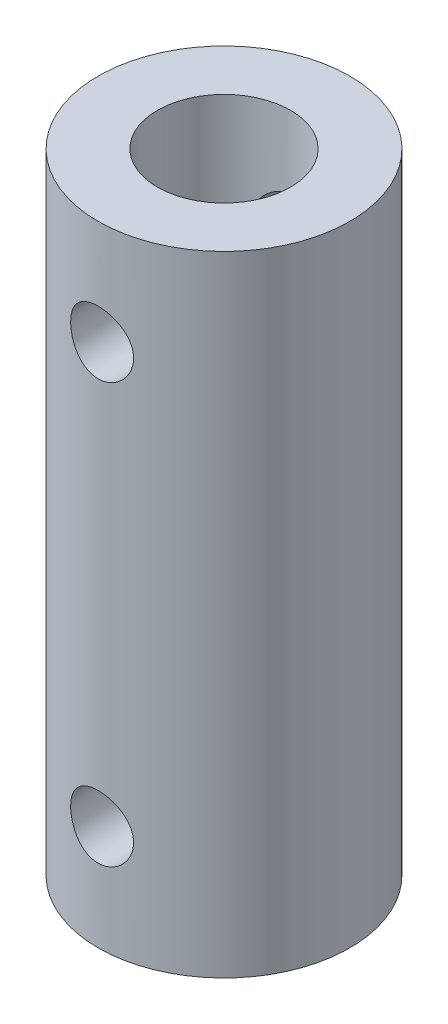
SolidWorks part; units mm, degrees
ref_plane "Front Plane" through (0, 0, 0) normal (0, 0, 1) x (1, 0, 0)
ref_plane "Top Plane" through (0, 0, 0) normal (0, 1, 0) x (1, 0, 0)
ref_plane "Right Plane" through (0, 0, 0) normal (1, 0, 0) x (0, 0, -1)
sketch "Sketch1" plane through (0, 0, 0) normal (0, 1, 0) x (1, 0, 0)
  circle A0 centre (0, 0) radius 6
  dimension "D1" = 12
extrude "Boss-Extrude1" add sketch "Sketch1" along normal blind 30
sketch "Sketch2" plane through (0, 30, 0) normal (0, 1, 0) x (1, 0, 0)
  circle A0 centre (0, 0) radius 3.175
  dimension "D1" = 6.35
extrude "Cut-Extrude1" cut sketch "Sketch2" against normal through all both and the other way through all
sketch "Sketch4" plane through (0, 0, 0) normal (0, 0, 1) x (1, 0, 0)
  line L0 (6, 30) -> (-6, 30) construction
  line L1 (-6, 0) -> (6, 0) construction
  circle A0 centre (0, 25) radius 1.5
  circle A1 centre (0, 5) radius 1.5
  dimension "D1" = 3
  dimension "D2" = 5
  dimension "D3" = 3
  dimension "D4" = 5
extrude "Cut-Extrude4" cut sketch "Sketch4" against normal through all both and the other way through all
